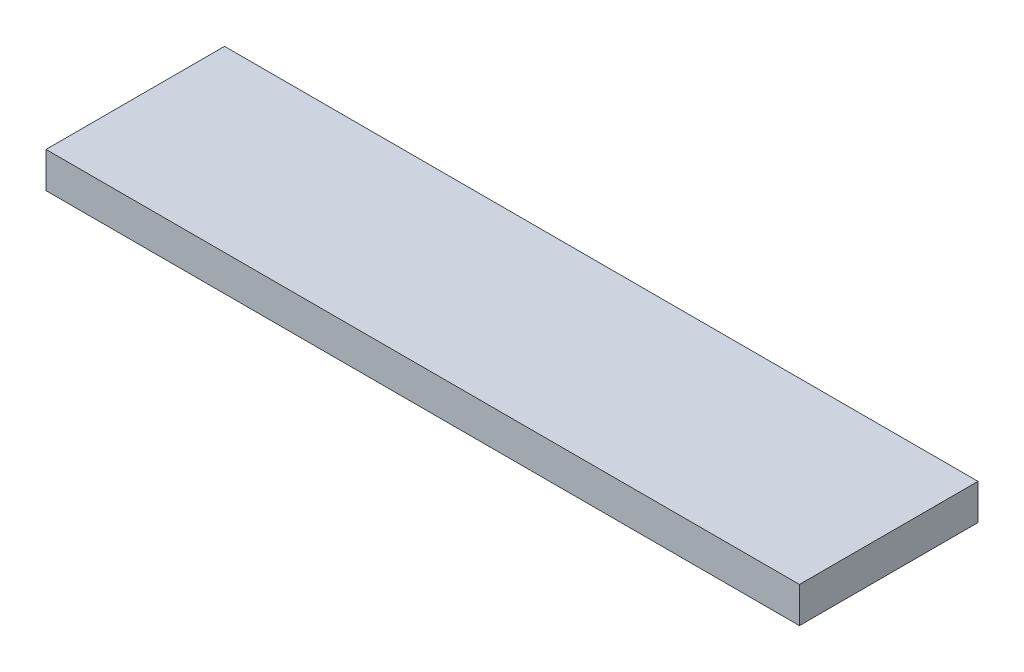
SolidWorks part; units mm, degrees
ref_plane "Front Plane" through (0, 0, 0) normal (0, 0, 1) x (1, 0, 0)
ref_plane "Top Plane" through (0, 0, 0) normal (0, 1, 0) x (1, 0, 0)
ref_plane "Right Plane" through (0, 0, 0) normal (1, 0, 0) x (0, 0, -1)
sketch "Sketch1" plane through (0, 0, 0) normal (0, 1, 0) x (1, 0, 0)
  line L1 (-31.65, -7.5) -> (31.65, -7.5)
  line L2 (-31.65, -7.5) -> (-31.65, 7.5)
  line L3 (-31.65, 7.5) -> (31.65, 7.5)
  line L4 (31.65, -7.5) -> (31.65, 7.5)
  line L5 (-31.65, -7.5) -> (31.65, 7.5) construction
  line L6 (-31.65, 7.5) -> (31.65, -7.5) construction
  point P0 (0, 0)
  dimension "D1" = 15
  dimension "D2" = 63.3
extrude "Boss-Extrude1" add sketch "Sketch1" along normal blind 3
